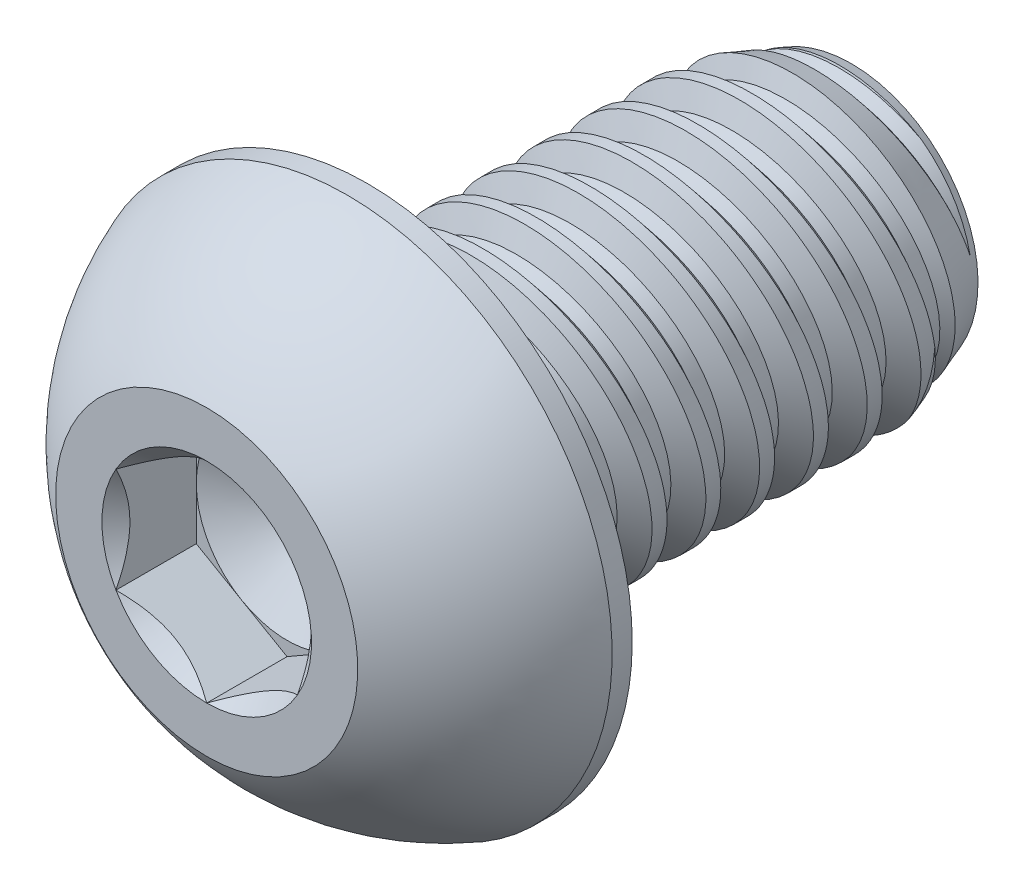
SolidWorks part; units mm, degrees
ref_plane "Front" through (0, 0, 0) normal (0, 0, 1) x (1, 0, 0)
ref_plane "Top" through (0, 0, 0) normal (0, 1, 0) x (1, 0, 0)
ref_plane "Right" through (0, 0, 0) normal (1, 0, 0) x (0, 0, -1)
sketch "Sketch1" plane through (0, 0, 0) normal (1, 0, 0) x (0, 0, -1)
  line L0 (0, 0) -> (-4.2164, 0) construction
  line L1 (0, 0) -> (12.7, 0)
  line L2 (0, 0) -> (0, 3.9624)
  line L3 (0, 3.9624) -> (12.7, 3.9624)
  line L4 (12.7, 0) -> (12.7, 3.9624)
  line L5 (0, -3.9624) -> (12.7, -3.9624) construction
  dimension "D1" = 12.7
  dimension "Thread Dia" = 7.9248
  dimension "Length" = 12.7
  dimension "Head Height" = 4.2164
revolve "Revolve1" add sketch "Sketch1" angle 360 about L0
ref_plane "Plane1" through (0, 0, 4.2164) normal (0, 0, 1) x (1, 0, 0)
sketch "Sketch2" plane through (0, 0, 0) normal (1, 0, 0) x (0, 0, -1)
  line L0 (0, 3.9624) -> (0, -3.9624) construction
  line L1 (0, -3.9624) -> (1.4111, -3.9624) construction
  line L2 (1.4111, -3.9624) -> (0, 3.9624) construction
  line L3 (0, 3.9624) -> (0.1737, 3.9933) construction
  line L4 (0.1737, 3.9933) -> (1.3893, 4.2098)
  line L5 (1.3893, 4.2098) -> (1.089, 3.3805)
  line L6 (1.089, 3.3805) -> (0.7417, 3.3187)
  line L7 (0.7417, 3.3187) -> (0.1737, 3.9933)
  line L8 (0.9154, 3.3496) -> (0.7815, 4.1015) construction
  line L9 (0, -3.9624) -> (12.7, -3.9624) construction
  line L10 (0, 3.9624) -> (12.7, 3.9624) construction
  line L12 (0.8062, 3.9624) -> (2.2173, -3.9624) construction
  line L13 (0, -0.2692) -> (3.0236, 0.2692) construction
  line L15 (0, 0) -> (0, 3.9624) construction
  point P19 (1.5118, 0)
  dimension "D1" = 60
  dimension "Thread Pitch" = 1.4111
  dimension "D2" = 0.1764
  dimension "D3" = 0.3528
  dimension "D4" = 1.4111
revolve "Cut-Revolve1" cut sketch "Sketch2" angle 360 about L13
sketch "Sketch3" plane through (0, 0, 0) normal (1, 0, 0) x (0, 0, -1)
  line L0 (12.7, 3.3187) -> (10.9314, 3.9624)
  line L1 (10.9314, 3.9624) -> (12.7, 3.9624)
  line L2 (12.7, 3.9624) -> (12.7, 3.3187)
  line L3 (0, 3.9624) -> (12.7, 3.9624) construction
  line L4 (12.7, 0) -> (12.7, 3.9624) construction
  line L5 (10.9314, 0) -> (0, 0) construction
  line L6 (10.9314, 3.9624) -> (10.9314, -3.9624) construction
  line L7 (0, -3.9624) -> (12.7, -3.9624) construction
  dimension "D1" = 20
  dimension "D2" = 7.9248
revolve "Cut-Revolve2" cut sketch "Sketch3" angle 360 about L5
pattern_linear "LPattern1" count 9 spacing 1.4111 along (0, 0, 1)
pattern_linear "LPattern2" count 2 spacing 1.4111 along (0, 0, 1)
sketch "Sketch4" plane through (0, 0, 0) normal (0, 0, 1) x (1, 0, 0)
  circle A0 centre (0, 0) radius 6.9469
  dimension "Head Dia" = 13.8938
extrude "Extrude1" add sketch "Sketch4" along normal up to surface (4.2164 mm away)
sketch "Sketch9" plane through (0, 0, 0) normal (1, 0, 0) x (0, 0, -1)
  line L0 (0, 6.9469) -> (-0.5271, 6.9469)
  line L1 (0, 6.9469) -> (0, 7.474)
  line L2 (0, 7.474) -> (-4.7435, 7.474)
  line L3 (0, 0) -> (-4.2164, 0) construction
  line L4 (-4.7435, 7.474) -> (-4.7435, 3.9624)
  line L5 (-4.7435, 3.9624) -> (-4.2164, 3.9624)
  line L6 (0, 0) -> (0, 3.9624) construction
  line L10 (0, 6.9469) -> (-4.2164, 6.9469) construction
  line L11 (0, 3.9624) -> (12.7, 3.9624) construction
  line L12 (-4.2164, 6.9469) -> (-4.2164, -6.9469) construction
  arc A0 (-4.2164, 3.9624) -> (-0.5271, 6.9469) centre (2.0408, 0) cw
  dimension "Side Head Height" = 0.5271
revolve "Cut-Revolve3" cut sketch "Sketch9" angle 360 about L3
sketch "Sketch6" plane through (0, 0, 4.2164) normal (0, 0, 1) x (1, 0, 0)
  line L1 (0, -2.7496) -> (2.3812, -1.3748)
  line L2 (2.3812, -1.3748) -> (2.3812, 1.3748)
  line L3 (2.3812, 1.3748) -> (0, 2.7496)
  line L4 (0, 2.7496) -> (-2.3813, 1.3748)
  line L5 (-2.3813, 1.3748) -> (-2.3813, -1.3748)
  line L6 (-2.3813, -1.3748) -> (0, -2.7496)
  circle A0 centre (0, 0) radius 2.3813 construction
  dimension "Hex" = 4.7625
extrude "Cut-Extrude1" cut sketch "Sketch6" against normal blind 2.1082
sketch "Sketch7" plane through (0, 0, 4.2164) normal (0, 0, 1) x (1, 0, 0)
  circle A0 centre (0, 0) radius 2.7496
extrude "Cut-Extrude4" cut sketch "Sketch7" against normal blind 2.1082 draft 45
sketch "Sketch8" plane through (0, 0, 2.1082) normal (0, 0, 1) x (1, 0, 0)
  circle A0 centre (0, 0) radius 2.3813 construction
  circle A1 centre (0, 0) radius 2.3813
extrude "Cut-Extrude5" cut sketch "Sketch8" against normal blind 0.7027 draft 60
equation "\"D2@Sketch2\"=\"Thread Pitch@Sketch2\"/8"
equation "\"D3@Sketch2\"=\"Thread Pitch@Sketch2\"/4"
equation "\"D4@Sketch2\"=\"Thread Pitch@Sketch2\""
equation "\"D3@LPattern1\"=\"Thread Pitch@Sketch2\""
equation "\"D1@Cut-Extrude1\"=\"Head Height@Sketch1\"/2"
equation "\"D1@Cut-Extrude4\"=\"D1@Cut-Extrude1\""
equation "\"D1@Cut-Extrude5\"=\"D1@Cut-Extrude1\"/3"
equation "\"D1@LPattern1\"=\"D1@Sketch1\"/\"Thread Pitch@Sketch2\""
equation "\"D3@LPattern2\"=\"Thread Pitch@Sketch2\""
equation "\"Side Head Height@Sketch9\"=\"Head Height@Sketch1\"/8"
